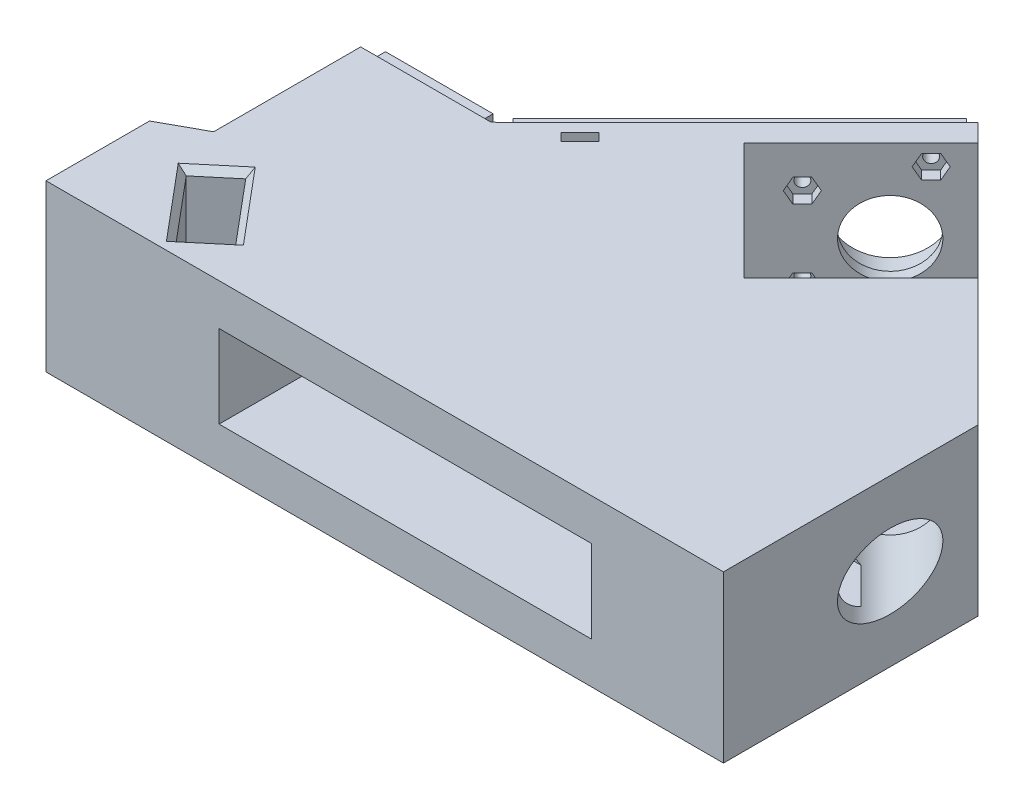
SolidWorks part; units mm, degrees
ref_plane "Спереди" through (0, 0, 0) normal (0, 0, 1) x (1, 0, 0)
ref_plane "Сверху" through (0, 0, 0) normal (0, 1, 0) x (1, 0, 0)
ref_plane "Справа" through (0, 0, 0) normal (1, 0, 0) x (0, 0, -1)
sketch "Sketch1" plane through (0, 0, 0) normal (0, 1, 0) x (1, 0, 0)
  line L0 (-79.5035, -54.4347) -> (-79.5035, -4.4347)
  line L1 (-79.5035, -54.4347) -> (60.4965, -54.4347)
  line L2 (-21.9513, 53.1175) -> (-14.8802, 46.0465)
  line L3 (-21.9513, 53.1175) -> (-46.7, 28.3688)
  line L4 (-14.8802, 46.0465) -> (-43.1645, 17.7622)
  line L5 (-43.1645, 17.7622) -> (-14.8802, -10.5221)
  line L6 (-14.8802, -10.5221) -> (13.404, 17.7622)
  line L7 (13.404, 17.7622) -> (60.4965, -29.3302)
  line L8 (60.4965, -29.3302) -> (60.4965, -54.4347)
  line L9 (-79.5035, -4.4347) -> (-46.7, 28.3688)
  dimension "D1" = 35
  dimension "D2" = 140
  dimension "D3" = 40
  dimension "D4" = 50
  dimension "D5" = 10
  dimension "D6" = 40
extrude "Boss-Extrude1" add sketch "Sketch1" along normal blind 40
sketch "Sketch3" plane through (-37.5344, 0, -37.5344) normal (-0.7071, 0, -0.7071) x (-0.7071, 0, 0.7071)
  line L0 (-22.0379, 20) -> (59.3533, 20) construction
  line L1 (-22.0379, 40) -> (-22.0379, 0) construction
  line L2 (59.3533, 40) -> (59.3533, 0) construction
  circle A0 centre (-7.0379, 20) radius 9
  dimension "D1" = 18
  dimension "D2" = 15
extrude "Cut-Extrude1" cut sketch "Sketch3" against normal through all
sketch "Sketch4" plane through (15.5831, 0, -15.5831) normal (0.7071, 0, -0.7071) x (-0.7071, 0, -0.7071)
  line L0 (3.0817, 20) -> (-63.517, 20) construction
  line L1 (3.0817, 40) -> (3.0817, 0) construction
  line L2 (-63.517, 40) -> (-63.517, 0) construction
  line L3 (-6.9183, 0) -> (-6.9183, 40) construction
  line L4 (-63.517, 0) -> (3.0817, 0) construction
  line L5 (-63.517, 40) -> (3.0817, 40) construction
  line L6 (-31.9183, 0) -> (-31.9183, 40) construction
  line L7 (-6.9183, 5) -> (-6.9183, 35)
  line L8 (-6.9183, 35) -> (-31.9183, 35)
  line L9 (-31.9183, 35) -> (-31.9183, 5)
  line L10 (-31.9183, 5) -> (-6.9183, 5)
  dimension "D1" = 10
  dimension "D2" = 25
  dimension "D3" = 5
  dimension "D4" = 5
extrude "Cut-Extrude2" cut sketch "Sketch4" against normal blind 30
sketch "Sketch5" plane through (-37.5344, 0, -37.5344) normal (-0.7071, 0, -0.7071) x (-0.7071, 0, 0.7071)
  circle A0 centre (-7.0379, 20) radius 11.1
  dimension "D1" = 22.2
extrude "Cut-Extrude3" cut sketch "Sketch5" against normal blind 7
sketch "Sketch6" plane through (4.892, 0, 4.892) normal (0.7071, 0, 0.7071) x (0.7071, 0, -0.7071)
  circle A0 centre (7.0379, 20) radius 11.1
  dimension "D1" = 22.2
extrude "Cut-Extrude4" cut sketch "Sketch6" against normal blind 7
sketch "Sketch7" plane through (0, 40, 0) normal (0, 1, 0) x (1, 0, 0)
  line L0 (44.1167, -12.9505) -> (44.1167, -54.4347)
  line L1 (60.4965, -29.3302) -> (13.404, 17.7622) construction
  line L2 (-79.5035, -54.4347) -> (60.4965, -54.4347) construction
  line L3 (44.1167, -54.4347) -> (60.4965, -54.4347)
  line L4 (60.4965, -54.4347) -> (60.4965, -29.3302)
  line L5 (60.4965, -29.3302) -> (44.1167, -12.9505)
extrude "Cut-Extrude5" cut sketch "Sketch7" against normal through all
sketch "Sketch9" plane through (-79.5035, 0, 0) normal (-1, 0, 0) x (0, 0, 1)
  line L0 (4.4347, 0) -> (54.4347, 0)
  line L1 (54.4347, 0) -> (54.4347, 40)
  line L2 (54.4347, 40) -> (4.4347, 40)
  line L3 (4.4347, 40) -> (4.4347, 0)
extrude "Boss-Extrude2" add sketch "Sketch9" along normal blind 30
sketch "Sketch11" plane through (-37.5344, 0, -37.5344) normal (-0.7071, 0, -0.7071) x (-0.7071, 0, 0.7071)
  line L0 (7.9621, 0) -> (7.9621, 40) construction
  line L1 (-22.0379, 0) -> (59.3533, 0) construction
  line L2 (-22.0379, 40) -> (59.3533, 40) construction
  circle A1 centre (7.9621, 10) radius 1.45
  circle A2 centre (7.9621, 30) radius 1.45
  circle A3 centre (-7.0379, 20) radius 11.1 construction
  point P10 (7.9621, 20)
  dimension "D1" = 20
  dimension "D4" = 2.9
  dimension "D2" = 10
  dimension "D3" = 15
extrude "Cut-Extrude8" cut sketch "Sketch11" against normal blind 20
sketch "Sketch13" plane through (0, 40, 0) normal (0, 1, 0) x (1, 0, 0)
  line L0 (-21.9513, 53.1175) -> (-57.0321, 88.7453) construction
  line L1 (-109.5035, -4.4347) -> (-109.5035, 36.2739) construction
  line L2 (-109.5035, 36.2739) -> (-57.0321, 88.7453) construction
  line L3 (-21.9513, 53.1175) -> (-79.5035, -4.4347) construction
  line L4 (-109.5035, -4.4347) -> (-79.5035, -4.4347) construction
  line L5 (-79.5035, -4.4347) -> (-21.9513, 53.1175) construction
  dimension "D1" = 50
  dimension "D2" = 74.2058
  dimension "D3" = 40.7086
  dimension "D4" = 135
  dimension "D5" = 30
  dimension "D6" = 81.3912
sketch "Sketch15" plane through (-37.5344, 0, -37.5344) normal (-0.7071, 0, -0.7071) x (-0.7071, 0, 0.7071)
  line L0 (-22.0379, 0) -> (59.3533, 40) construction
  line L1 (-22.0379, 40) -> (-22.0379, 0) construction
  line L2 (57.3533, 38) -> (-20.0379, 38)
  line L3 (57.3533, 38) -> (57.3533, 2)
  line L4 (57.3533, 2) -> (-20.0379, 2)
  line L5 (-20.0379, 38) -> (-20.0379, 2)
  line L6 (57.3533, 38) -> (-20.0379, 2) construction
  line L7 (57.3533, 2) -> (-20.0379, 38) construction
  line L8 (-22.0379, 0) -> (59.3533, 0) construction
  line L10 (59.3533, 40) -> (-22.0379, 40)
  line L11 (59.3533, 40) -> (59.3533, 0)
  line L12 (59.3533, 0) -> (-22.0379, 0)
  line L13 (-22.0379, 40) -> (-22.0379, 0)
  line L14 (59.3533, 40) -> (-22.0379, 0) construction
  line L15 (59.3533, 0) -> (-22.0379, 40) construction
  point P4 (18.6577, 20)
  point P13 (18.6577, 20)
  dimension "D1" = 2
  dimension "D2" = 2
extrude "Cut-Extrude9" cut sketch "Sketch15" against normal blind 4
sketch "Sketch16" plane through (0, 0, 4.4347) normal (0, 0, -1) x (-1, 0, 0)
  line L0 (79.5035, 0) -> (109.5035, 40) construction
  line L2 (109.5035, 40) -> (79.5035, 40)
  line L3 (109.5035, 40) -> (109.5035, 0)
  line L4 (109.5035, 0) -> (79.5035, 0)
  line L5 (79.5035, 40) -> (79.5035, 0)
  line L6 (109.5035, 40) -> (79.5035, 0) construction
  line L7 (109.5035, 0) -> (79.5035, 40) construction
  line L8 (107.5035, 38) -> (81.5035, 38)
  line L9 (107.5035, 38) -> (107.5035, 2)
  line L10 (107.5035, 2) -> (81.5035, 2)
  line L11 (81.5035, 38) -> (81.5035, 2)
  line L12 (107.5035, 38) -> (81.5035, 2) construction
  line L13 (107.5035, 2) -> (81.5035, 38) construction
  point P4 (94.5035, 20)
  point P5 (94.5035, 20)
  dimension "D1" = 2
  dimension "D2" = 2
extrude "Cut-Extrude10" cut sketch "Sketch16" against normal blind 4
sketch "Sketch17" plane through (0, 0, 0) normal (0, -1, 0) x (1, 0, 0)
  line L0 (-76.6751, 7.2631) -> (-78.0893, 8.4347)
  line L1 (-78.0893, 8.4347) -> (-79.5035, 8.4347)
  line L2 (-79.5035, 8.4347) -> (-109.5035, 8.4347) construction
  line L3 (-76.6751, 7.2631) -> (-79.5035, 4.4347)
  line L4 (-79.5035, 4.4347) -> (-79.5035, 8.4347)
extrude "Cut-Extrude11" cut sketch "Sketch17" against normal through all
sketch "Sketch18" plane through (0, 40, 0) normal (0, 1, 0) x (1, 0, 0)
  line L0 (-109.5035, -54.4347) -> (-109.5035, -74.4347)
  line L1 (-109.5035, -74.4347) -> (44.1167, -74.4347)
  line L2 (44.1167, -74.4347) -> (44.1167, -54.4347)
  line L3 (44.1167, -54.4347) -> (-109.5035, -54.4347)
  dimension "D1" = 20
extrude "Boss-Extrude3" add sketch "Sketch18" against normal up to surface (40 mm away) up to face at (-33.1074, 0, 2.2377)
sketch "Sketch10" plane through (0, 40, 0) normal (0, 1, 0) x (1, 0, 0)
  line L0 (-109.5035, -59.4347) -> (44.1167, -59.4347) construction
  line L1 (-109.5035, -74.4347) -> (-109.5035, -8.4347) construction
  line L2 (44.1167, -12.9505) -> (44.1167, -74.4347) construction
  line L3 (-92.1081, -70.45) -> (-105.0924, -54.9759)
  line L4 (-99.8184, -69.5597) -> (-89.5684, -69.5597) construction
  line L5 (-99.8184, -69.5597) -> (-99.8184, -49.3097) construction
  line L6 (-99.8184, -49.3097) -> (-89.5684, -49.3097) construction
  line L7 (-89.5684, -69.5597) -> (-89.5684, -49.3097) construction
  line L8 (-99.8184, -69.5597) -> (-89.5684, -49.3097) construction
  line L9 (-99.8184, -49.3097) -> (-89.5684, -69.5597) construction
  line L10 (34.4316, -69.5597) -> (24.1816, -69.5597) construction
  line L11 (34.4316, -69.5597) -> (34.4316, -49.3097) construction
  line L12 (34.4316, -49.3097) -> (24.1816, -49.3097) construction
  line L13 (24.1816, -69.5597) -> (24.1816, -49.3097) construction
  line L14 (34.4316, -69.5597) -> (24.1816, -49.3097) construction
  line L15 (34.4316, -49.3097) -> (24.1816, -69.5597) construction
  line L16 (-92.1081, -70.45) -> (-84.2944, -63.8935)
  line L17 (-105.0924, -54.9759) -> (-97.2787, -48.4194)
  line L18 (-84.2944, -63.8935) -> (-97.2787, -48.4194)
  line L19 (-101.1856, -51.6977) -> (-88.2013, -67.1718) construction
  line L20 (-98.6002, -62.7129) -> (-90.7866, -56.1565) construction
  line L21 (-109.5035, -74.4347) -> (-109.5035, -8.4347) construction
  line L22 (31.8919, -70.45) -> (18.9076, -54.9759) construction
  line L23 (31.8919, -70.45) -> (39.7056, -63.8935) construction
  line L24 (18.9076, -54.9759) -> (26.7213, -48.4194) construction
  line L25 (39.7056, -63.8935) -> (26.7213, -48.4194) construction
  line L26 (22.8144, -51.6977) -> (35.7987, -67.1718) construction
  line L27 (25.3998, -62.7129) -> (33.2134, -56.1565) construction
  line L28 (44.1167, -12.9505) -> (44.1167, -74.4347) construction
  point P6 (-94.6934, -59.4347)
  point P11 (29.3066, -59.4347)
  point P17 (-94.6934, -59.4347)
  point P18 (-32.6934, -59.4347)
  point P24 (29.3066, -59.4347)
  dimension "D1" = 10.25
  dimension "D2" = 20.25
  dimension "D3" = 15
  dimension "D4" = 62
  dimension "D5" = 62
  dimension "D6" = 14.8101
  dimension "D7" = 10.2
  dimension "D8" = 20.2
  dimension "D9" = 40
  dimension "D10" = 20.2
  dimension "D11" = 10.2
  dimension "D12" = 40
extrude "Cut-Extrude7" cut sketch "Sketch10" against normal through all
sketch "Sketch19" plane through (-109.5035, 0, 0) normal (-1, 0, 0) x (0, 0, 1)
  line L0 (8.4347, 20) -> (74.4347, 20) construction
  line L1 (8.4347, 0) -> (8.4347, 40) construction
  line L2 (74.4347, 0) -> (74.4347, 40) construction
  line L4 (43.9347, 27.5) -> (28.9347, 27.5)
  line L5 (43.9347, 27.5) -> (43.9347, 12.5)
  line L6 (43.9347, 12.5) -> (28.9347, 12.5)
  line L7 (28.9347, 27.5) -> (28.9347, 12.5)
  line L8 (43.9347, 27.5) -> (28.9347, 12.5) construction
  line L9 (43.9347, 12.5) -> (28.9347, 27.5) construction
  point P6 (36.4347, 20)
  dimension "D1" = 15
  dimension "D2" = 15
  dimension "D3" = 38
extrude "Cut-Extrude12" cut sketch "Sketch19" against normal blind 150
sketch "Sketch20" plane through (-37.5344, 0, -37.5344) normal (-0.7071, 0, -0.7071) x (-0.7071, 0, 0.7071)
  line L0 (-20.0379, 5) -> (57.3533, 5) construction
  line L1 (-20.0379, 38) -> (-20.0379, 2) construction
  line L2 (57.3533, 2) -> (57.3533, 38) construction
  line L3 (-20.0379, 35) -> (57.3533, 35) construction
  line L4 (-14.0379, 5) -> (-14.0379, 35) construction
  line L5 (45.9621, 5) -> (45.9621, 35) construction
  line L7 (-22.0379, 40) -> (-22.0379, 0) construction
  circle A0 centre (45.9621, 5) radius 1.45
  circle A1 centre (45.9621, 35) radius 1.45
  circle A2 centre (-14.0379, 35) radius 1.45
  circle A3 centre (-14.0379, 5) radius 1.45
  point P8 (-20.0379, 20)
  point P17 (-14.0379, 20)
  dimension "D3" = 2.9
  dimension "D1" = 30
  dimension "D2" = 15
  dimension "D4" = 60
  dimension "D5" = 8
extrude "Cut-Extrude13" cut sketch "Sketch20" against normal blind 20
sketch "Sketch30" plane through (-109.5035, 0, 0) normal (-1, 0, 0) x (0, 0, 1)
  line L0 (74.4347, 20) -> (86.6307, 20) construction
  line L1 (74.4347, 0) -> (74.4347, 40) construction
  line L3 (86.6307, 89.9728) -> (74.4347, 89.9728)
  line L4 (86.6307, 89.9728) -> (86.6307, -49.9728)
  line L5 (86.6307, -49.9728) -> (74.4347, -49.9728)
  line L6 (74.4347, 89.9728) -> (74.4347, -49.9728)
  line L7 (86.6307, 89.9728) -> (74.4347, -49.9728) construction
  line L8 (86.6307, -49.9728) -> (74.4347, 89.9728) construction
  point P4 (80.5327, 20)
sketch "Sketch31" plane through (-37.5344, 0, -37.5344) normal (-0.7071, 0, -0.7071) x (-0.7071, 0, 0.7071)
  line L0 (7.9621, 10) -> (7.9621, 30) construction
  line L1 (7.9621, 20) -> (-7.0379, 20) construction
  dimension "D1" = 15
  dimension "D2" = 20
sketch "Sketch36" plane through (-30.4633, 0, -30.4633) normal (0.7071, 0, 0.7071) x (0.7071, 0, -0.7071)
  line L0 (22.0379, 40) -> (22.0379, 0) construction
  line L1 (12.4129, 37.8146) -> (10.7879, 35)
  line L2 (10.7879, 35) -> (12.4129, 32.1854)
  line L3 (12.4129, 32.1854) -> (15.6629, 32.1854)
  line L4 (15.6629, 32.1854) -> (17.2879, 35)
  line L5 (17.2879, 35) -> (15.6629, 37.8146)
  line L6 (15.6629, 37.8146) -> (12.4129, 37.8146)
  line L7 (15.6629, 7.8146) -> (12.4129, 7.8146)
  line L8 (12.4129, 7.8146) -> (10.7879, 5)
  line L9 (10.7879, 5) -> (12.4129, 2.1854)
  line L10 (12.4129, 2.1854) -> (15.6629, 2.1854)
  line L11 (15.6629, 2.1854) -> (17.2879, 5)
  line L12 (17.2879, 5) -> (15.6629, 7.8146)
  line L13 (-6.3371, 32.8146) -> (-9.5871, 32.8146)
  line L14 (-9.5871, 32.8146) -> (-11.2121, 30)
  line L15 (-11.2121, 30) -> (-9.5871, 27.1854)
  line L16 (-9.5871, 27.1854) -> (-6.3371, 27.1854)
  line L17 (-6.3371, 27.1854) -> (-4.7121, 30)
  line L18 (-4.7121, 30) -> (-6.3371, 32.8146)
  line L19 (-6.3371, 12.8146) -> (-9.5871, 12.8146)
  line L20 (-9.5871, 12.8146) -> (-11.2121, 10)
  line L21 (-11.2121, 10) -> (-9.5871, 7.1854)
  line L22 (-9.5871, 7.1854) -> (-6.3371, 7.1854)
  line L23 (-6.3371, 7.1854) -> (-4.7121, 10)
  line L24 (-4.7121, 10) -> (-6.3371, 12.8146)
  circle A0 centre (14.0379, 35) radius 3.25 construction
  circle A1 centre (14.0379, 5) radius 3.25 construction
  circle A2 centre (-7.9621, 30) radius 3.25 construction
  circle A3 centre (-7.9621, 10) radius 3.25 construction
  dimension "D1" = 6.5
extrude "Cut-Extrude16" cut sketch "Sketch36" against normal blind 3
sketch "Sketch37" plane through (-37.5344, 0, -37.5344) normal (-0.7071, 0, -0.7071) x (-0.7071, 0, 0.7071)
  line L0 (49.2121, 5) -> (49.2121, 0)
  line L1 (42.7121, 35) -> (44.3371, 32.1854)
  line L2 (44.3371, 32.1854) -> (47.5871, 32.1854)
  line L3 (47.5871, 32.1854) -> (49.2121, 35)
  line L4 (49.2121, 35) -> (47.5871, 37.8146) construction
  line L5 (47.5871, 37.8146) -> (44.3371, 37.8146) construction
  line L6 (44.3371, 37.8146) -> (42.7121, 35) construction
  line L7 (42.7121, 5) -> (44.3371, 2.1854) construction
  line L8 (44.3371, 2.1854) -> (47.5871, 2.1854) construction
  line L9 (47.5871, 2.1854) -> (49.2121, 5) construction
  line L10 (49.2121, 5) -> (47.5871, 7.8146)
  line L11 (47.5871, 7.8146) -> (44.3371, 7.8146)
  line L12 (44.3371, 7.8146) -> (42.7121, 5)
  line L13 (49.2121, 0) -> (42.7121, 0)
  line L14 (42.7121, 0) -> (42.7121, 5)
  line L15 (42.7121, 35) -> (42.7121, 40)
  line L16 (42.7121, 40) -> (49.2121, 40)
  line L17 (49.2121, 40) -> (49.2121, 35)
  line L18 (-22.0379, 0) -> (59.3533, 0) construction
  line L19 (59.3533, 40) -> (-22.0379, 40) construction
  circle A0 centre (45.9621, 35) radius 3.25 construction
  circle A1 centre (45.9621, 5) radius 3.25 construction
  dimension "D1" = 6.5
extrude "Cut-Extrude18" cut sketch "Sketch37" against normal blind 2.55 from offset 7 offset against normal yes
sketch "Sketch38" plane through (0, 0, 74.4347) normal (0, 0, 1) x (1, 0, 0)
  line L0 (44.1167, 20) -> (-109.5035, 20) construction
  line L1 (44.1167, 0) -> (44.1167, 40) construction
  line L3 (12.3066, 10) -> (-77.6934, 10)
  line L4 (12.3066, 10) -> (12.3066, 30)
  line L5 (12.3066, 30) -> (-77.6934, 30)
  line L6 (-77.6934, 10) -> (-77.6934, 30)
  line L7 (12.3066, 10) -> (-77.6934, 30) construction
  line L8 (12.3066, 30) -> (-77.6934, 10) construction
  point P5 (-32.6934, 20)
  point P12 (-32.6934, 20)
  dimension "D1" = 20
  dimension "D2" = 90
extrude "Cut-Extrude19" cut sketch "Sketch38" against normal up to surface (45.5 mm away) up to face at (-40.2488, 20, 28.9347)
sketch "Sketch39" plane through (-109.5035, 0, 0) normal (-1, 0, 0) x (0, 0, 1)
  line L0 (28.9347, 10) -> (13.9681, 20)
  line L1 (13.9681, 20) -> (28.9347, 30)
  line L2 (28.9347, 30) -> (28.9347, 10)
  line L3 (28.9347, 27.5) -> (28.9347, 12.5) construction
  point P9 (28.9347, 20)
  point P10 (28.9347, 20)
  dimension "D1" = 20
  dimension "D2" = 18
  dimension "D3" = 20
extrude "Cut-Extrude21" cut sketch "Sketch39" against normal up to surface (90 mm away) from vertex at -31.8101 up to face at (12.3066, 20, 44.0597) starting at point (-77.6934, 12.5, 28.9347)
sketch "Sketch42" plane through (0, 40, 0) normal (0, 1, 0) x (1, 0, 0)
  line L0 (-109.5035, -43.9347) -> (-109.5035, -74.4347)
  line L1 (-109.5035, -74.4347) -> (-109.5035, -8.4347) construction
  line L2 (-109.5035, -74.4347) -> (-119.5035, -74.4347)
  line L3 (-119.5035, -74.4347) -> (-119.5035, -49.4347)
  line L4 (-119.5035, -49.4347) -> (-109.5035, -43.9347)
  dimension "D1" = 10
  dimension "D2" = 25
extrude "Boss-Extrude11" add sketch "Sketch42" against normal up to surface (40 mm away) up to face at (-33.1074, 0, 5.874)
chamfer "Chamfer1" distance 1.5 angle 45 8 edges at (-101.1856, 40, 51.6977) (-101.1856, 0, 51.6977) (-98.6002, 40, 62.7129) (-98.6002, 0, 62.7129) (-88.2013, 40, 67.1718) (-88.2013, 0, 67.1718) (-90.7866, 40, 56.1565) (-90.7866, 0, 56.1565)
